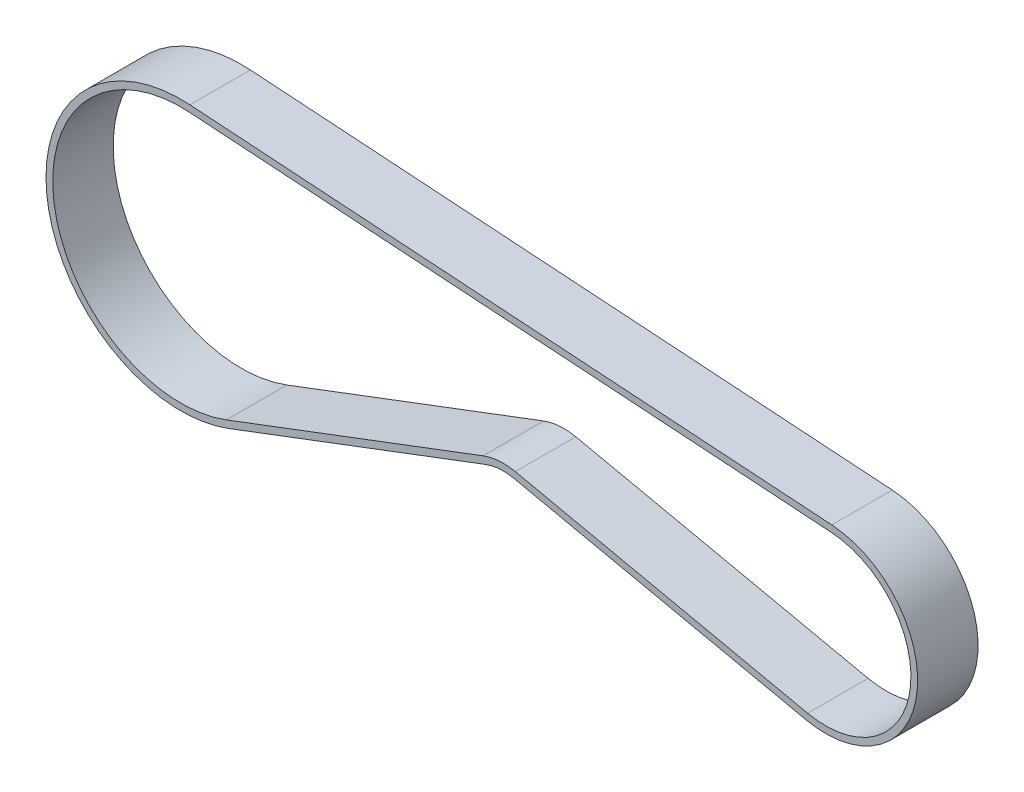
SolidWorks part; units mm, degrees
material "NEOPRENE"
ref_plane "Front Plane" through (0, 0, 0) normal (0, 0, 1) x (1, 0, 0)
ref_plane "Top Plane" through (0, 0, 0) normal (0, 1, 0) x (1, 0, 0)
ref_plane "Right Plane" through (0, 0, 0) normal (1, 0, 0) x (0, 0, -1)
sketch "Sketch1" plane through (0, 0, 0) normal (0, 0, 1) x (1, 0, 0)
  line L0 (-51.0105, -3.3851) -> (-89.2352, -17.8619)
  line L1 (-46.2078, -3.0252) -> (-2.6778, -12.4145)
  line L2 (0.8467, 12.6717) -> (-94.7267, 19.0575)
  line L3 (-96, 0) -> (0, 0) construction
  line L4 (0, 0) -> (-48, -11.3341) construction
  line L5 (-48, -11.3341) -> (-96, 0) construction
  line L6 (0.9133, 13.6695) -> (-94.66, 20.0553)
  line L7 (-50.6563, -4.3203) -> (-88.881, -18.7971)
  line L8 (-46.4186, -4.0027) -> (-2.8886, -13.392)
  arc A0 (0.8467, 12.6717) -> (-2.6778, -12.4145) centre (0, 0) cw
  arc A1 (-94.7267, 19.0575) -> (-89.2352, -17.8619) centre (-96, 0) ccw
  arc A2 (-46.2078, -3.0252) -> (-51.0105, -3.3851) centre (-48, -11.3341) ccw
  arc A3 (-94.66, 20.0553) -> (-88.881, -18.7971) centre (-96, 0) ccw
  arc A4 (-46.4186, -4.0027) -> (-50.6563, -4.3203) centre (-48, -11.3341) ccw
  arc A5 (0.9133, 13.6695) -> (-2.8886, -13.392) centre (0, 0) cw
  dimension "D4" = 8.5
  dimension "D5" = 12.7
  dimension "D6" = 19.1
  dimension "D1" = 96
  dimension "D2" = 49.32
  dimension "D3" = 49.32
  dimension "D7" = 1
extrude "Boss-Extrude1" add sketch "Sketch1" along normal mid plane 9
